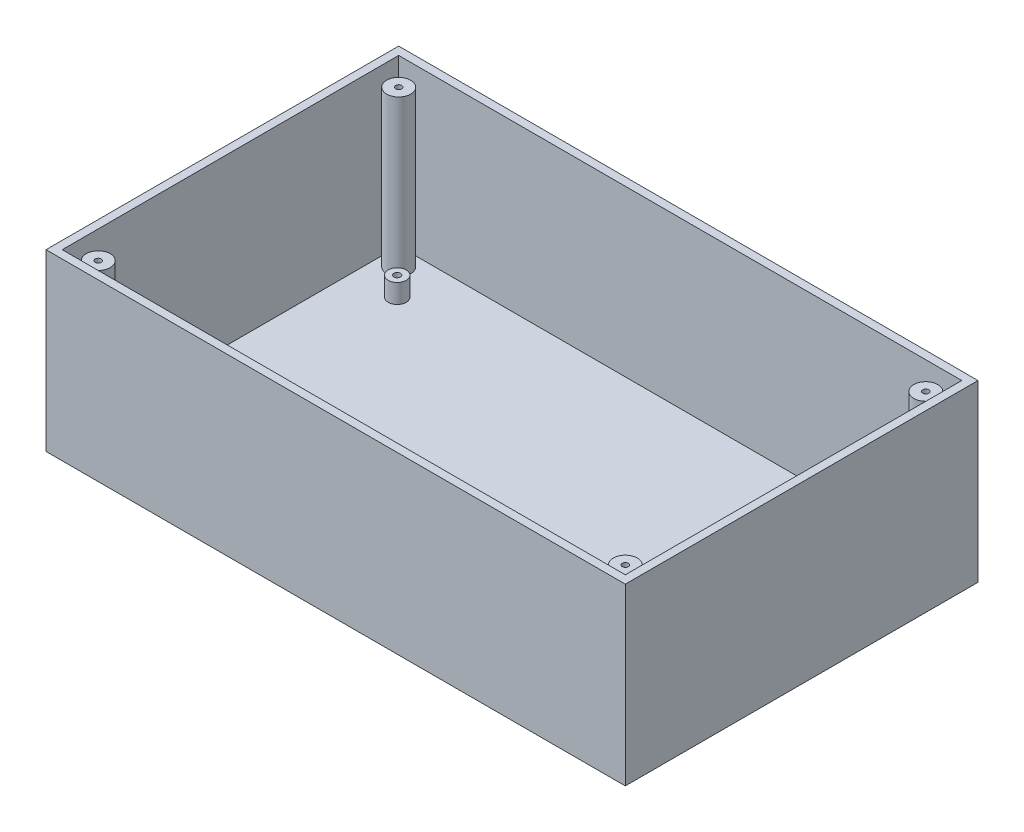
SolidWorks part; units mm, degrees
ref_plane "Front Plane" through (0, 0, 0) normal (0, 0, 1) x (1, 0, 0)
ref_plane "Top Plane" through (0, 0, 0) normal (0, 1, 0) x (1, 0, 0)
ref_plane "Right Plane" through (0, 0, 0) normal (1, 0, 0) x (0, 0, -1)
sketch "Sketch1" plane through (0, 0, 0) normal (0, 1, 0) x (1, 0, 0)
  line L1 (0, 0) -> (193, 0)
  line L2 (0, 0) -> (0, 117.5)
  line L3 (0, 117.5) -> (193, 117.5)
  line L4 (193, 0) -> (193, 117.5)
  dimension "D1" = 117.5
  dimension "D2" = 193
extrude "Boss-Extrude1" add sketch "Sketch1" along normal blind 3.22
sketch "Sketch3" plane through (0, 3.22, 0) normal (0, 1, 0) x (1, 0, 0)
  line L0 (2.7, 2.7) -> (2.7, 114.8)
  line L1 (0, 0) -> (193, 0)
  line L2 (0, 0) -> (0, 117.5)
  line L3 (0, 117.5) -> (193, 117.5)
  line L4 (193, 0) -> (193, 117.5)
  line L5 (2.7, 114.8) -> (190.3, 114.8)
  line L6 (190.3, 2.7) -> (190.3, 114.8)
  line L7 (2.7, 2.7) -> (190.3, 2.7)
  dimension "D1" = 2.7
extrude "Boss-Extrude2" add sketch "Sketch3" along normal blind 55
sketch "Sketch4" plane through (0, 3.22, 0) normal (0, 1, 0) x (1, 0, 0)
  line L0 (2.7, 2.7) -> (190.3, 2.7) construction
  line L1 (0, 0) -> (193, 0) construction
  line L2 (96.5, 0) -> (96.5, 117.5) construction
  line L3 (193, 117.5) -> (0, 117.5) construction
  line L4 (0, 58.75) -> (193, 58.75) construction
  line L5 (0, 117.5) -> (0, 0) construction
  line L6 (193, 0) -> (193, 117.5) construction
  line L7 (2.7, 114.8) -> (2.7, 2.7) construction
  circle A0 centre (17.2, 17.7) radius 3
  circle A1 centre (17.2, 17.7) radius 1.1
  circle A2 centre (175.8, 17.7) radius 1.1
  circle A3 centre (175.8, 17.7) radius 3
  circle A4 centre (17.2, 99.8) radius 1.1
  circle A5 centre (17.2, 99.8) radius 3
  circle A6 centre (175.8, 99.8) radius 3
  circle A7 centre (175.8, 99.8) radius 1.1
  dimension "D1" = 6
  dimension "D2" = 2.2
  dimension "D3" = 15
  dimension "D4" = 14.5
extrude "Boss-Extrude3" add sketch "Sketch4" along normal blind 6.36
sketch "Sketch6" plane through (0, 3.22, 0) normal (0, 1, 0) x (1, 0, 0)
  line L0 (96.5, 117.5) -> (96.5, 2.7)
  line L1 (193, 117.5) -> (0, 117.5) construction
  line L2 (2.7, 2.7) -> (190.3, 2.7) construction
  line L3 (2.7, 58.75) -> (190.3, 58.75)
  line L4 (2.7, 114.8) -> (2.7, 2.7) construction
  line L5 (190.3, 2.7) -> (190.3, 114.8) construction
  line L6 (2.7, 2.7) -> (190.3, 2.7) construction
  line L7 (2.7, 114.8) -> (2.7, 2.7) construction
  circle A0 centre (8.7, 8.7) radius 1
  circle A1 centre (8.7, 8.7) radius 4
  circle A2 centre (8.7, 108.8) radius 4
  circle A3 centre (8.7, 108.8) radius 1
  circle A4 centre (184.3, 108.8) radius 1
  circle A5 centre (184.3, 108.8) radius 4
  circle A6 centre (184.3, 8.7) radius 4
  circle A7 centre (184.3, 8.7) radius 1
  dimension "D1" = 2
  dimension "D2" = 8
  dimension "D3" = 6
  dimension "D4" = 6
extrude "Boss-Extrude4" add sketch "Sketch6" along normal offset from surface (51.84 mm away) 3.16 contours A1 A0 | A6 A7 | A5 A4 | A2 A3 up to face at (96.5, 58.22, -58.75)
sketch "Sketch7" plane through (0, 3.22, 0) normal (0, 1, 0) x (1, 0, 0)
  line L0 (0, 117.5) -> (0, 0) construction
  line L1 (0, 0) -> (193, 0) construction
  line L2 (0, 117.5) -> (0, 0)
  line L3 (0, 0) -> (193, 0)
  circle A0 centre (45, 45) radius 4.7625
  dimension "D1" = 45
  dimension "D3" = 9.525
  dimension "D2" = 45
extrude "Cut-Extrude1" cut sketch "Sketch7" against normal through all both and the other way through all contours A0
hole_wizard "1/4 Clearance Hole1" positions "Sketch9" profile "Sketch8" hole size "1/4" standard "ANSI Inch" end condition through all
sketch "Sketch9" plane through (0, 3.22, 0) normal (0, 1, 0) x (1, 0, 0)
  line L0 (31.99, 45) -> (58.01, 45) construction
  point P0 (58.01, 45)
  point P2 (31.99, 45)
  point P11 (45, 45)
  dimension "D1" = 26.02
sketch "Sketch8" plane through (58.01, 3.22, -45) normal (1, 0, 0) x (0, 0, 1)
  line L0 (0, 0) -> (0, 3.22)
  line L1 (0, 3.22) -> (3.3782, 3.22)
  line L2 (3.3782, 3.22) -> (3.3782, 0)
  line L5 (3.3782, 0) -> (0, 0)
  line L11 (0, -6.35) -> (0, 107.95) construction
  dimension "Thru Hole Dia." = 6.7564
  dimension "Thru Hole Depth" = 3.22
